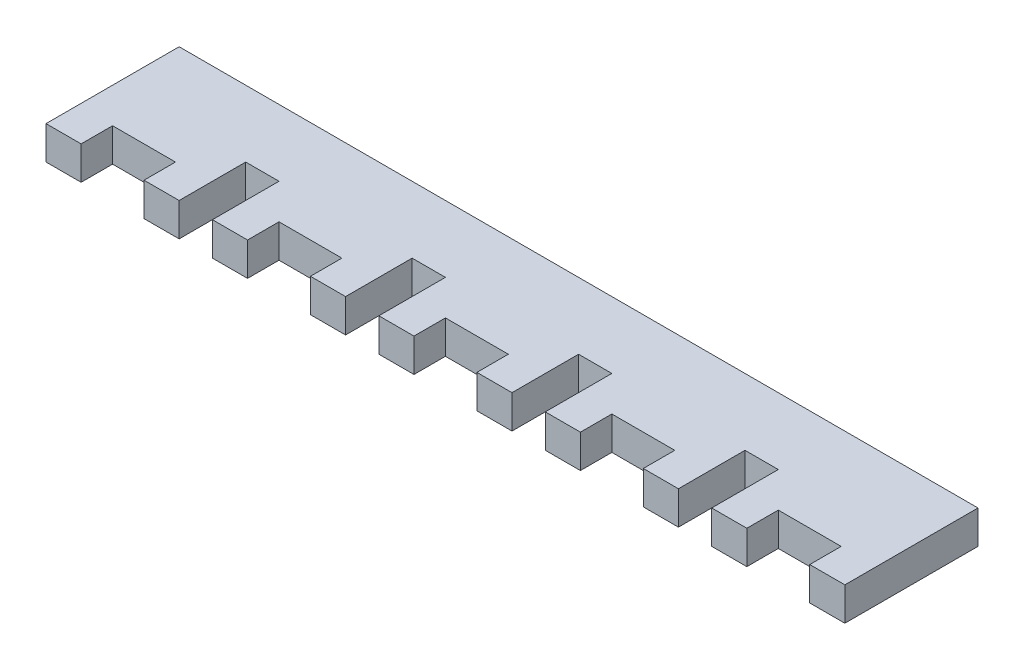
SolidWorks part; units mm, degrees
ref_plane "Front Plane" through (0, 0, 0) normal (0, 0, 1) x (1, 0, 0)
ref_plane "Top Plane" through (0, 0, 0) normal (0, 1, 0) x (1, 0, 0)
ref_plane "Right Plane" through (0, 0, 0) normal (1, 0, 0) x (0, 0, -1)
sketch "Sketch1" plane through (0, 0, 0) normal (0, 1, 0) x (1, 0, 0)
  line L1 (0, 0) -> (76.2, 0)
  line L2 (0, 0) -> (0, -12.7)
  line L3 (0, -12.7) -> (76.2, -12.7)
  line L4 (76.2, 0) -> (76.2, -12.7)
extrude "Boss-Extrude1" add sketch "Sketch1" along normal blind 3.175
sketch "Sketch3" plane through (0, 3.175, 0) normal (0, 1, 0) x (1, 0, 0)
  line L0 (0, 0) -> (0, -12.7) construction
  line L5 (76.2, 0) -> (0, 0) construction
  line L6 (0, -12.7) -> (76.2, -12.7) construction
  line L7 (0, -6.35) -> (12.7, -6.35) construction
  line L8 (12.7, 0) -> (12.7, -12.7) construction
  line L9 (12.7, -6.35) -> (15.875, -6.35) construction
  line L10 (15.875, 0) -> (15.875, -12.7) construction
sketch "Sketch4" plane through (0, 3.175, 0) normal (0, 1, 0) x (1, 0, 0)
  line L0 (12.7, -6.35) -> (12.7, -12.7)
  line L1 (12.7, -6.35) -> (15.875, -6.35)
  line L2 (15.875, -6.35) -> (15.875, -12.7)
  line L3 (12.7, -12.7) -> (15.875, -12.7)
extrude "Cut-Extrude1" cut sketch "Sketch4" against normal through all
pattern_linear "LPattern1" count 4 spacing 15.875 along (1, 0, 0) of "Cut-Extrude1"
sketch "Sketch5" plane through (0, 3.175, 0) normal (0, 1, 0) x (1, 0, 0)
  line L2 (0, -12.7) -> (12.7, -12.7) construction
  line L3 (6.35, -9.7) -> (9.35, -9.7)
  line L9 (9.35, -9.7) -> (9.35, -12.7)
  line L10 (9.35, -12.7) -> (3.35, -12.7)
  line L11 (3.35, -12.7) -> (3.35, -9.7)
  line L12 (3.35, -9.7) -> (6.35, -9.7)
extrude "Cut-Extrude2" cut sketch "Sketch5" against normal through all
pattern_linear "LPattern2" count 5 spacing 15.875 along (1, 0, 0) of "Cut-Extrude2"
